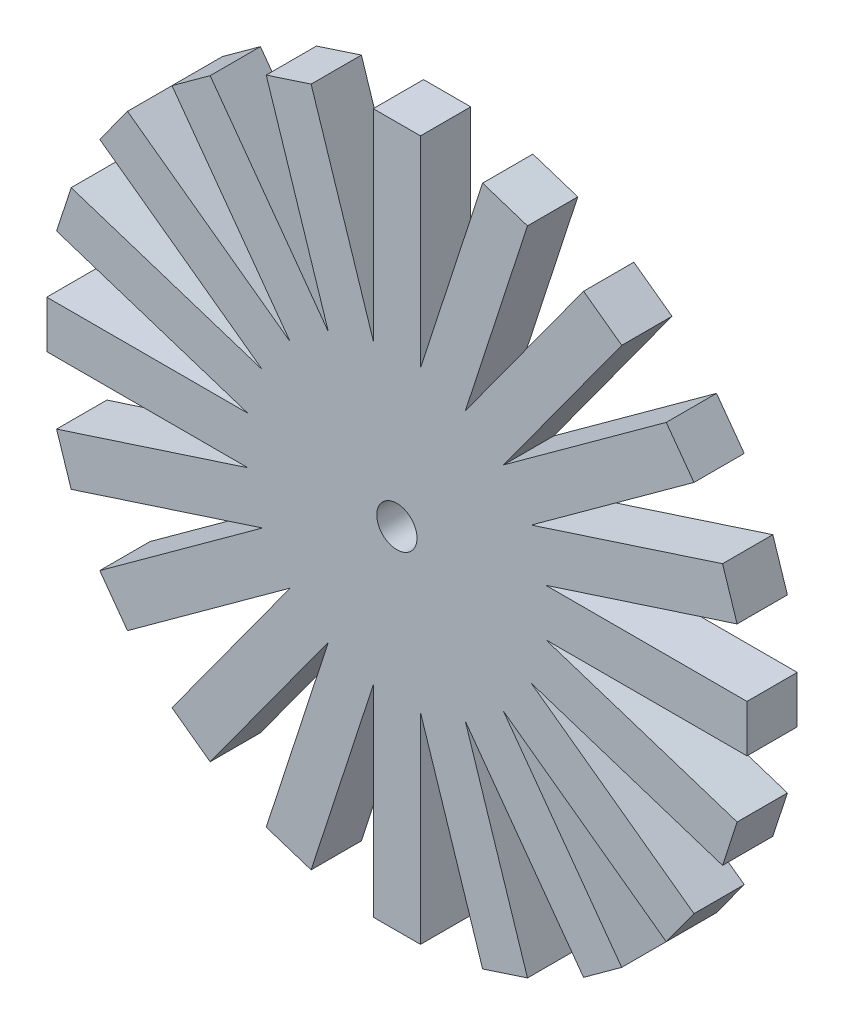
SolidWorks part; units mm, degrees
ref_plane "Plan de face" through (0, 0, 0) normal (0, 0, 1) x (1, 0, 0)
ref_plane "Plan de dessus" through (0, 0, 0) normal (0, 1, 0) x (1, 0, 0)
ref_plane "Plan de droite" through (0, 0, 0) normal (1, 0, 0) x (0, 0, -1)
sketch "Esquisse1" plane through (0, 0, 0) normal (0, 0, 1) x (1, 0, 0)
  line L0 (0, 15) -> (0, -15) construction
  line L1 (-15, 0) -> (15, 0) construction
  line L2 (-14.8153, -2.3465) -> (-34.8153, -2.3465)
  line L3 (-34.8153, -2.3465) -> (-34.8153, 2.3465)
  line L4 (-14.8153, 2.3465) -> (-34.8153, 2.3465)
  line L5 (0, 0) -> (-14.8153, 2.3465) construction
  line L6 (-13.3651, 6.8099) -> (-32.3862, 12.9902)
  line L7 (-33.8365, 8.5269) -> (-32.3862, 12.9902)
  line L8 (-14.8153, 2.3465) -> (-33.8365, 8.5269)
  line L9 (-10.6066, 10.6066) -> (-26.7869, 22.3623)
  line L10 (-29.5454, 18.5656) -> (-26.7869, 22.3623)
  line L11 (-13.3651, 6.8099) -> (-29.5454, 18.5656)
  line L12 (-6.8099, 13.3651) -> (-18.5656, 29.5454)
  line L13 (-22.3623, 26.7869) -> (-18.5656, 29.5454)
  line L14 (-10.6066, 10.6066) -> (-22.3623, 26.7869)
  line L15 (-2.3465, 14.8153) -> (-8.5269, 33.8365)
  line L16 (-12.9902, 32.3862) -> (-8.5269, 33.8365)
  line L17 (-6.8099, 13.3651) -> (-12.9902, 32.3862)
  line L18 (2.3465, 14.8153) -> (2.3465, 34.8153)
  line L19 (-2.3465, 34.8153) -> (2.3465, 34.8153)
  line L20 (-2.3465, 14.8153) -> (-2.3465, 34.8153)
  line L21 (6.8099, 13.3651) -> (12.9902, 32.3862)
  line L22 (8.5269, 33.8365) -> (12.9902, 32.3862)
  line L23 (2.3465, 14.8153) -> (8.5269, 33.8365)
  line L24 (10.6066, 10.6066) -> (22.3623, 26.7869)
  line L25 (18.5656, 29.5454) -> (22.3623, 26.7869)
  line L26 (6.8099, 13.3651) -> (18.5656, 29.5454)
  line L27 (13.3651, 6.8099) -> (29.5454, 18.5656)
  line L28 (26.7869, 22.3623) -> (29.5454, 18.5656)
  line L29 (10.6066, 10.6066) -> (26.7869, 22.3623)
  line L30 (14.8153, 2.3465) -> (33.8365, 8.5269)
  line L31 (32.3862, 12.9902) -> (33.8365, 8.5269)
  line L32 (13.3651, 6.8099) -> (32.3862, 12.9902)
  line L33 (14.8153, -2.3465) -> (34.8153, -2.3465)
  line L34 (34.8153, 2.3465) -> (34.8153, -2.3465)
  line L35 (14.8153, 2.3465) -> (34.8153, 2.3465)
  line L36 (13.3651, -6.8099) -> (32.3862, -12.9902)
  line L37 (33.8365, -8.5269) -> (32.3862, -12.9902)
  line L38 (14.8153, -2.3465) -> (33.8365, -8.5269)
  line L39 (10.6066, -10.6066) -> (26.7869, -22.3623)
  line L40 (29.5454, -18.5656) -> (26.7869, -22.3623)
  line L41 (13.3651, -6.8099) -> (29.5454, -18.5656)
  line L42 (6.8099, -13.3651) -> (18.5656, -29.5454)
  line L43 (22.3623, -26.7869) -> (18.5656, -29.5454)
  line L44 (10.6066, -10.6066) -> (22.3623, -26.7869)
  line L45 (2.3465, -14.8153) -> (8.5269, -33.8365)
  line L46 (12.9902, -32.3862) -> (8.5269, -33.8365)
  line L47 (6.8099, -13.3651) -> (12.9902, -32.3862)
  line L48 (-2.3465, -14.8153) -> (-2.3465, -34.8153)
  line L49 (2.3465, -34.8153) -> (-2.3465, -34.8153)
  line L50 (2.3465, -14.8153) -> (2.3465, -34.8153)
  line L51 (-6.8099, -13.3651) -> (-12.9902, -32.3862)
  line L52 (-8.5269, -33.8365) -> (-12.9902, -32.3862)
  line L53 (-2.3465, -14.8153) -> (-8.5269, -33.8365)
  line L54 (-10.6066, -10.6066) -> (-22.3623, -26.7869)
  line L55 (-18.5656, -29.5454) -> (-22.3623, -26.7869)
  line L56 (-6.8099, -13.3651) -> (-18.5656, -29.5454)
  line L57 (-13.3651, -6.8099) -> (-29.5454, -18.5656)
  line L58 (-26.7869, -22.3623) -> (-29.5454, -18.5656)
  line L59 (-10.6066, -10.6066) -> (-26.7869, -22.3623)
  line L60 (-14.8153, -2.3465) -> (-33.8365, -8.5269)
  line L61 (-32.3862, -12.9902) -> (-33.8365, -8.5269)
  line L62 (-13.3651, -6.8099) -> (-32.3862, -12.9902)
  circle A0 centre (0, 0) radius 15
  circle A1 centre (0, 0) radius 2
  point P12 (-34.8153, 0)
  dimension "D1" = 30
  dimension "D5" = 4
  dimension "D2" = 9
  dimension "D3" = 20
  dimension "D4" = 20
extrude "Boss.-Extru.1" add sketch "Esquisse1" along normal blind 5
